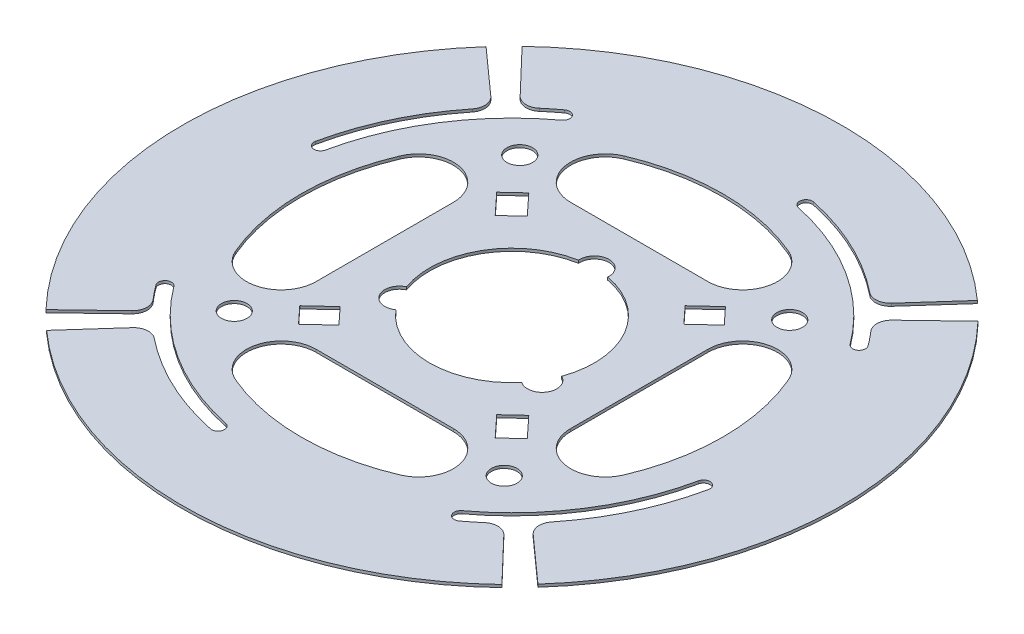
SolidWorks part; units mm, degrees
ref_plane "Front Plane" through (0, 0, 0) normal (0, 0, 1) x (1, 0, 0)
ref_plane "Top Plane" through (0, 0, 0) normal (0, 1, 0) x (1, 0, 0)
ref_plane "Right Plane" through (0, 0, 0) normal (1, 0, 0) x (0, 0, -1)
sketch "Sketch1" plane through (0, 0, 0) normal (0, 1, 0) x (1, 0, 0)
  line L0 (0, 0) -> (0, 90) construction
  line L1 (0, 0) -> (-26.3044, 26.3044) construction
  line L5 (-18.75, 34.75) -> (18.75, 34.75)
  line L6 (0, 0.0636) -> (60, 67.082) construction
  line L7 (60, 67.082) -> (65, 62.2495) construction
  line L8 (65, 62.2495) -> (0, 0.0636) construction
  line L9 (60, 67.082) -> (46.3261, 51.8087)
  line L10 (65, 62.2495) -> (50.1872, 48.078)
  circle A0 centre (0, 0) radius 22.5
  circle A1 centre (0, 0) radius 67.75 construction
  circle A2 centre (0, 0) radius 75.75 construction
  circle A3 centre (0, 0) radius 90
  arc A6 (-22.4609, 52.9952) -> (22.4609, 52.9952) centre (0, 0.0636) cw
  arc A7 (-22.4609, 52.9952) -> (-18.75, 34.75) centre (-18.75, 44.25) ccw
  arc A8 (22.4609, 52.9952) -> (18.75, 34.75) centre (18.75, 44.25) cw
  arc A9 (14, 66.2877) -> (54.4049, 40.3754) centre (0, 0) cw construction
  arc A10 (55.8101, 41.4183) -> (50.1872, 48.078) centre (0, 0) ccw
  arc A11 (52.9996, 39.3325) -> (13.6384, 64.5755) centre (0, 0) ccw
  arc A12 (52.9996, 39.3325) -> (55.8101, 41.4183) centre (54.4049, 40.3754) ccw
  arc A13 (14.3616, 68) -> (13.6384, 64.5755) centre (14, 66.2877) ccw
  circle A14 centre (0, 22.5) radius 4
  circle A15 centre (19.4856, -11.25) radius 4
  circle A16 centre (-19.4856, -11.25) radius 4
  arc A17 (46.3261, 51.8087) -> (14.3616, 68) centre (0, 0) ccw
  arc A18 (60, 67.082) -> (65, 62.2495) centre (0, 0) cw
  point P25 (36.5741, 57.0298)
  point P43 (0, 0)
  dimension "D1" = 180
  dimension "D2" = 151.5
  dimension "D3" = 135.5
  dimension "D4" = 45
  dimension "D10" = 57.5
  dimension "D13" = 1.75
  dimension "D16" = 8
  dimension "D5" = 45
  dimension "D6" = 37.2
  dimension "D11" = 14
  dimension "D12" = 48
  dimension "D14" = 60
  dimension "D15" = 65
  dimension "D17" = 3
sketch "Sketch2" plane through (0, 0, 0) normal (0, 1, 0) x (1, 0, 0)
  circle A0 centre (19.4856, -11.25) radius 4 construction
  circle A1 centre (-19.4856, -11.25) radius 4 construction
  circle A2 centre (0, 0) radius 22.5 construction
  circle A3 centre (0, 22.5) radius 4 construction
  circle A4 centre (0, 0) radius 90 construction
  circle A5 centre (19.4856, -11.25) radius 4
  circle A6 centre (-19.4856, -11.25) radius 4
  circle A7 centre (0, 0) radius 22.5
  circle A8 centre (0, 22.5) radius 4
  circle A9 centre (0, 0) radius 90
extrude "Boss-Extrude1" add sketch "Sketch2" along normal blind 0.75 contours A9 A8 A7 A5 A6
sketch "Sketch4" plane through (0, 0.75, 0) normal (0, 1, 0) x (1, 0, 0)
  line L0 (-18.75, 34.75) -> (18.75, 34.75) construction
  line L1 (-18.75, 34.75) -> (18.75, 34.75)
  arc A0 (18.75, 34.75) -> (22.4609, 52.9952) centre (18.75, 44.25) ccw construction
  arc A1 (-22.4609, 52.9952) -> (-18.75, 34.75) centre (-18.75, 44.25) ccw construction
  arc A2 (22.4609, 52.9952) -> (-22.4609, 52.9952) centre (0, 0.0636) ccw construction
  arc A3 (18.75, 34.75) -> (22.4609, 52.9952) centre (18.75, 44.25) ccw
  arc A4 (-22.4609, 52.9952) -> (-18.75, 34.75) centre (-18.75, 44.25) ccw
  arc A5 (22.4609, 52.9952) -> (-22.4609, 52.9952) centre (0, 0.0636) ccw
extrude "Cut-Extrude2" cut sketch "Sketch4" against normal blind 0.75
sketch "Sketch7" plane through (0, 0.75, 0) normal (0, 1, 0) x (1, 0, 0)
  line L0 (65, 62.2495) -> (50.1872, 48.078) construction
  line L1 (60, 67.082) -> (46.3261, 51.8087) construction
  line L2 (65, 62.2495) -> (50.1872, 48.078)
  line L3 (60, 67.082) -> (46.3261, 51.8087)
  arc A0 (52.9996, 39.3325) -> (55.8101, 41.4183) centre (54.4049, 40.3754) ccw construction
  arc A1 (55.8101, 41.4183) -> (50.1872, 48.078) centre (0, 0) ccw construction
  arc A2 (52.9996, 39.3325) -> (13.6384, 64.5755) centre (0, 0) ccw construction
  arc A3 (14.3616, 68) -> (13.6384, 64.5755) centre (14, 66.2877) ccw construction
  arc A4 (46.3261, 51.8087) -> (14.3616, 68) centre (0, 0) ccw construction
  arc A5 (52.9996, 39.3325) -> (55.8101, 41.4183) centre (54.4049, 40.3754) ccw
  arc A6 (55.8101, 41.4183) -> (50.1872, 48.078) centre (0, 0) ccw
  arc A7 (52.9996, 39.3325) -> (13.6384, 64.5755) centre (0, 0) ccw
  arc A8 (14.3616, 68) -> (13.6384, 64.5755) centre (14, 66.2877) ccw
  arc A9 (46.3261, 51.8087) -> (14.3616, 68) centre (0, 0) ccw
  circle M11 centre (0, 0) radius 90
extrude "Cut-Extrude6" cut sketch "Sketch7" against normal blind 0.75 and the other way through all contours L3 A9 A8 A7 A5 A6 L2 M11
sketch "Sketch8" plane through (0, 0.75, 0) normal (0, 1, 0) x (1, 0, 0)
  line L8 (-25.9255, 21.3368) -> (-31.2293, 27.0561)
  line L9 (-25.9255, 21.3368) -> (-21.3794, 25.5527)
  line L10 (-31.2293, 27.0561) -> (-26.6833, 31.2719)
  line L11 (-21.3794, 25.5527) -> (-26.6833, 31.2719)
  line L12 (-25.9255, 21.3368) -> (-26.6833, 31.2719) construction
  line L13 (-31.2293, 27.0561) -> (-21.3794, 25.5527) construction
  point P1 (-26.3044, 26.3044)
  dimension "D1" = 6.2
  dimension "D2" = 7.8
extrude "Cut-Extrude7" cut sketch "Sketch8" against normal blind 0.75
fillet "Fillet1" radius 4 2 edges at (50.1872, 0.375, -48.078) (46.3261, 0.375, -51.8087)
pattern_circular "CirPattern1" count 4 over 360 about axis through (0, 0, 0) along (0, 1, 0) of "Cut-Extrude7", "Cut-Extrude2"
pattern_circular "CirPattern2" count 4 over 360 about axis through (0, 0, 0) along (0, 1, 0) of "Cut-Extrude6", "Fillet1"
sketch "Sketch9" plane through (0, 0.75, 0) normal (0, 1, 0) x (1, 0, 0)
  line L0 (0, 0) -> (-26.3044, 26.3044) construction
  circle A2 centre (-36.8608, 38.9821) radius 3.5
  dimension "D1" = 53.65
  dimension "D2" = 7
  dimension "D3" = 1.5
extrude "Cut-Extrude8" cut sketch "Sketch9" against normal blind 0.75
pattern_circular "CirPattern3" count 4 over 360 about axis through (0, 0, 0) along (0, 1, 0) of "Cut-Extrude8"
